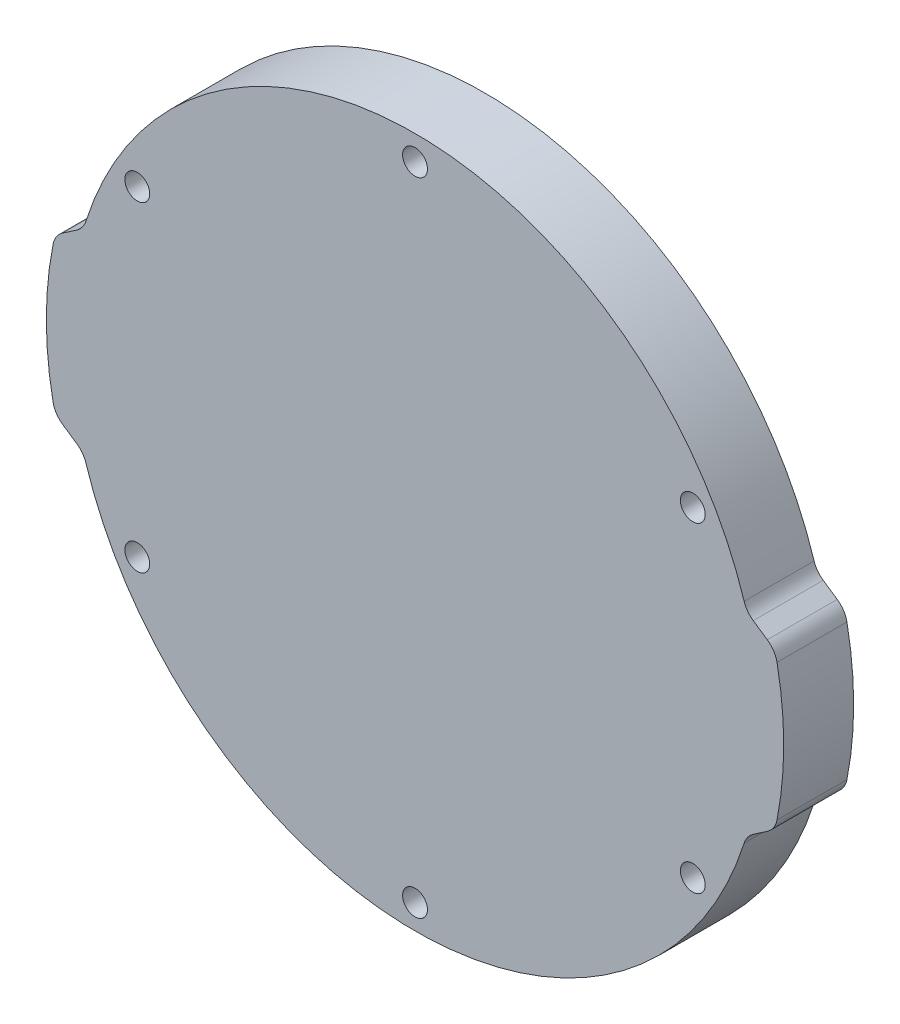
SolidWorks part; units mm, degrees
material "ABS PC"
ref_plane "Front Plane" through (0, 0, 0) normal (0, 0, 1) x (1, 0, 0)
ref_plane "Top Plane" through (0, 0, 0) normal (0, 1, 0) x (1, 0, 0)
ref_plane "Right Plane" through (0, 0, 0) normal (1, 0, 0) x (0, 0, -1)
sketch "Sketch1" plane through (0, 0, 0) normal (0, 0, 1) x (1, 0, 0)
  line L0 (-46.3248, 10) -> (-42.6562, 12.5)
  line L1 (-46.3248, -10) -> (-42.6562, -12.5)
  line L2 (46.3248, 10) -> (42.6562, 12.5)
  line L3 (46.3248, -10) -> (42.6562, -12.5)
  line L4 (0, 0) -> (35.7452, 20.6375) construction
  line L5 (35.7452, 20.6375) -> (38.4948, 22.225) construction
  line L6 (0, 41.275) -> (0, 0) construction
  line L7 (-47.5, 0) -> (0, 0) construction
  line L8 (0, 0) -> (47.5, 0) construction
  arc A0 (-42.6562, -12.5) -> (42.6562, -12.5) centre (0, 0) ccw
  circle A1 centre (0, 41.275) radius 1.6
  circle A2 centre (35.7452, 20.6375) radius 1.6
  circle A3 centre (35.7452, -20.6375) radius 1.6
  circle A4 centre (0, -41.275) radius 1.6
  circle A5 centre (-35.7452, -20.6375) radius 1.6
  circle A6 centre (-35.7452, 20.6375) radius 1.6
  arc A7 (-46.3248, 10) -> (-46.3248, -10) centre (-2.45, 0) ccw
  arc A8 (46.3248, 10) -> (46.3248, -10) centre (2.45, 0) cw
  arc A9 (42.6562, 12.5) -> (-42.6562, 12.5) centre (0, 0) ccw
  circle A10 centre (-47.5, 0) radius 1.6 construction
  circle A11 centre (-47.5, 0) radius 2.5 construction
  arc A12 (-42.6562, 12.5) -> (-42.6562, -12.5) centre (0, 0) ccw construction
  circle A13 centre (47.5, 0) radius 1.6 construction
  arc A14 (42.6562, 12.5) -> (42.6562, -12.5) centre (0, 0) cw construction
  point P17 (0, 0)
  point P19 (-47.45, 0)
  dimension "D1" = 88.9
  dimension "D2" = 3.175
  dimension "D3" = 3.2
  dimension "D6" = 3
  dimension "D11" = 3.2
  dimension "D12" = 5
  dimension "D14" = 45
  dimension "D5" = 25
  dimension "D7" = 20
  dimension "D9" = 3.175
  dimension "D10" = 60
  dimension "D13" = 47.5
  dimension "D4" = 6
extrude "Boss-Extrude1" add sketch "Sketch1" along normal blind 9
fillet "Fillet1" radius 3 8 edges at (42.6562, 12.5, 4.5) (42.6562, -12.5, 4.5) (-42.6562, -12.5, 4.5) (-46.3248, -10, 4.5) (-42.6562, 12.5, 4.5) (-46.3248, 10, 4.5) (46.3248, -10, 4.5) (46.3248, 10, 4.5)
